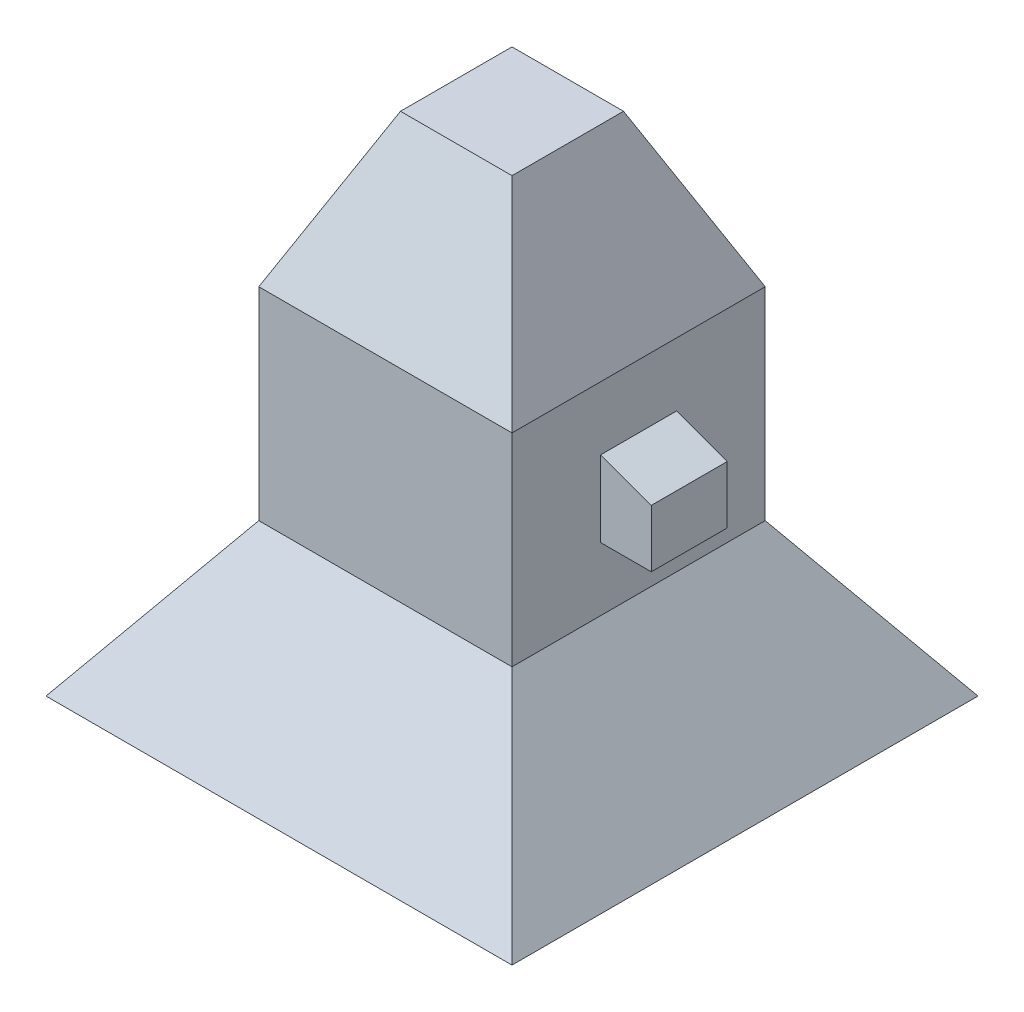
SolidWorks part; units mm, degrees
ref_plane "Front Plane" through (0, 0, 0) normal (0, 0, 1) x (1, 0, 0)
ref_plane "Top Plane" through (0, 0, 0) normal (0, 1, 0) x (1, 0, 0)
ref_plane "Right Plane" through (0, 0, 0) normal (1, 0, 0) x (0, 0, -1)
sketch "Sketch1" plane through (0, 0, 0) normal (0, 1, 0) x (1, 0, 0)
  line L1 (0, 0) -> (2540, 0)
  line L2 (0, 0) -> (0, 2540)
  line L3 (0, 2540) -> (2540, 2540)
  line L4 (2540, 0) -> (2540, 2540)
  line L5 (0, 0) -> (2540, 2540) construction
  line L6 (0, 2540) -> (2540, 0) construction
  point P4 (1270, 1270)
  dimension "D1" = 2540
extrude "Boss-Extrude1" add sketch "Sketch1" along normal blind 2032
sketch "Sketch3" plane through (0, 2032, 0) normal (0, 1, 0) x (1, 0, 0)
  line L4 (0, 2540) -> (0, 0)
  line L5 (0, 0) -> (2540, 0)
  line L6 (2540, 0) -> (2540, 2540)
  line L7 (2540, 2540) -> (0, 2540)
  line L8 (0, 2540) -> (0, 0)
  line L9 (0, 0) -> (2540, 0)
  line L10 (2540, 0) -> (2540, 2540)
  line L11 (2540, 2540) -> (0, 2540)
  dimension "D1" = 0
extrude "Boss-Extrude2" add sketch "Sketch3" along normal blind 1524 draft 25
sketch "Sketch6" plane through (0, 0, 0) normal (0, -1, 0) x (1, 0, 0)
  line L4 (0, 0) -> (0, -2540)
  line L5 (0, -2540) -> (2540, -2540)
  line L6 (2540, -2540) -> (2540, 0)
  line L7 (2540, 0) -> (0, 0)
  line L8 (0, 0) -> (0, -2540)
  line L9 (0, -2540) -> (2540, -2540)
  line L10 (2540, -2540) -> (2540, 0)
  line L11 (2540, 0) -> (0, 0)
  dimension "D1" = 0
extrude "Boss-Extrude3" add sketch "Sketch6" along normal blind 1524 draft 35 draft outward yes
sketch "Sketch7" plane through (0, -1524, 0) normal (0, -1, 0) x (1, 0, 0)
  line L0 (3607.1163, 1067.1163) -> (-1067.1163, 1067.1163) construction
  line L1 (-559.1163, 559.1163) -> (3099.1163, 559.1163)
  line L2 (-559.1163, 559.1163) -> (-559.1163, -3099.1163)
  line L3 (-559.1163, -3099.1163) -> (3099.1163, -3099.1163)
  line L4 (3099.1163, 559.1163) -> (3099.1163, -3099.1163)
  line L5 (-559.1163, 559.1163) -> (3099.1163, -3099.1163) construction
  line L6 (-559.1163, -3099.1163) -> (3099.1163, 559.1163) construction
  line L7 (3607.1163, -1270) -> (-1067.1163, -1270) construction
  line L8 (3607.1163, -3607.1163) -> (3607.1163, 1067.1163) construction
  line L9 (-1067.1163, 1067.1163) -> (-1067.1163, -3607.1163) construction
  point P4 (1270, -1270)
  point P14 (1270, -1270)
  dimension "D1" = 508
extrude "Cut-Extrude1" cut sketch "Sketch7" against normal blind 508 draft 35
sketch "Sketch8" plane through (2540, 0, 0) normal (1, 0, 0) x (0, 0, -1)
  line L0 (0, 1016) -> (2540, 1016) construction
  line L1 (889, 1397) -> (1651, 1397)
  line L2 (889, 1397) -> (889, 635)
  line L3 (889, 635) -> (1651, 635)
  line L4 (1651, 1397) -> (1651, 635)
  line L5 (1270, 635) -> (1270, 1397) construction
  line L6 (889, 1016) -> (1651, 1016) construction
  line L7 (0, 2032) -> (0, 0) construction
  line L8 (2540, 2032) -> (2540, 0) construction
  point P0 (1270, 1016)
  point P10 (1270, 1016)
  dimension "D1" = 762
extrude "Boss-Extrude4" add sketch "Sketch8" along normal blind 508
draft "Draft1" type of draft neutral plane draft angle 20 faces to draft 1 face at (2794, 1397, -1270) neutral plane through (2540, 2032, 0) neutral plane normal (1, 0, 0) parameters "D1"=20
equation "\"20degdeg\"=1"
